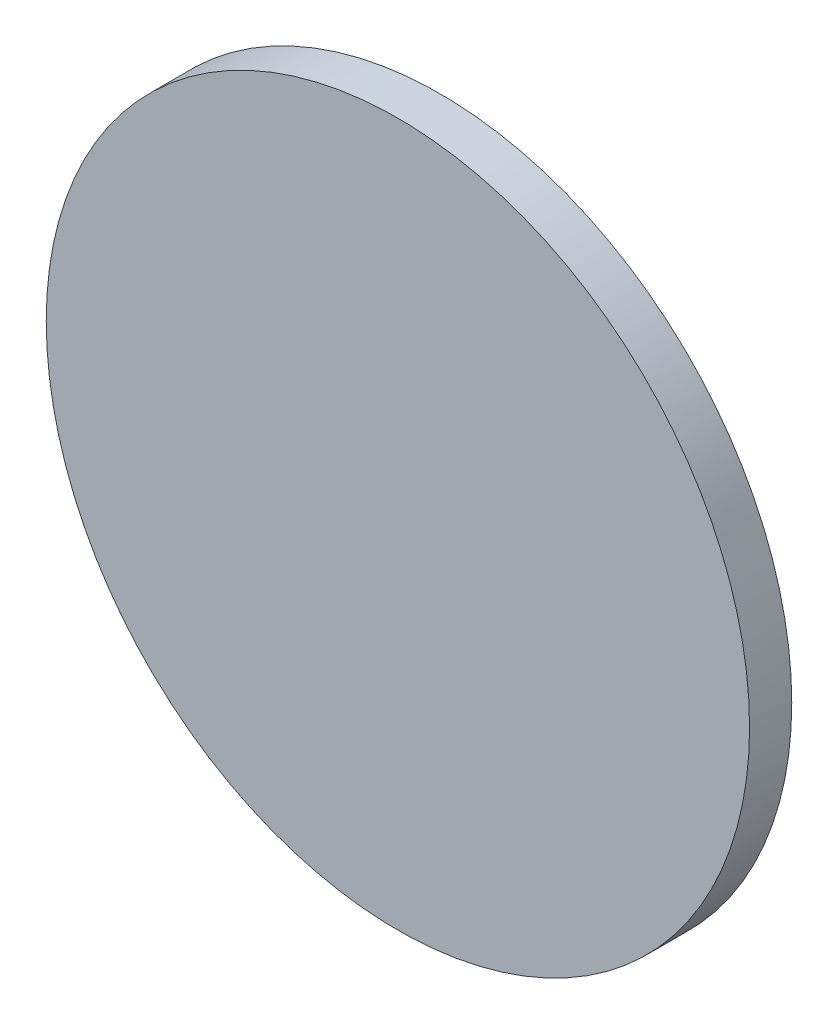
SolidWorks part; units mm, degrees
ref_plane "Front Plane" through (0, 0, 0) normal (0, 0, 1) x (1, 0, 0)
ref_plane "Top Plane" through (0, 0, 0) normal (0, 1, 0) x (1, 0, 0)
ref_plane "Right Plane" through (0, 0, 0) normal (1, 0, 0) x (0, 0, -1)
sketch "Sketch1" plane through (0, 0, 0) normal (0, 0, 1) x (1, 0, 0)
  circle A0 centre (0, 0) radius 44.45
  dimension "D1" = 88.9
extrude "Boss-Extrude1" add sketch "Sketch1" along normal mid plane 5.334
